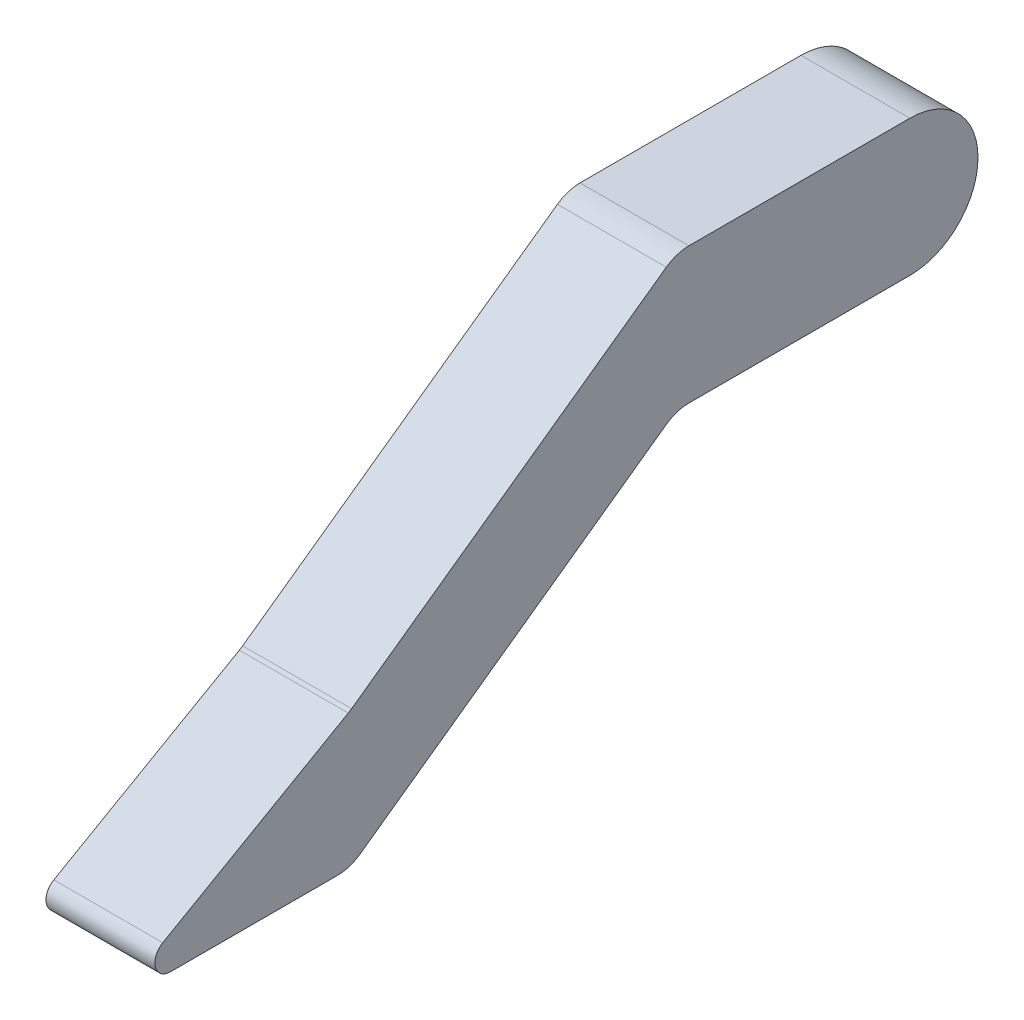
SolidWorks part; units mm, degrees
material "Oak"
ref_plane "Front Plane" through (0, 0, 0) normal (0, 0, 1) x (1, 0, 0)
ref_plane "Top Plane" through (0, 0, 0) normal (0, 1, 0) x (1, 0, 0)
ref_plane "Right Plane" through (0, 0, 0) normal (1, 0, 0) x (0, 0, -1)
sketch "Sketch1" plane through (0, 0, 0) normal (1, 0, 0) x (0, 0, -1)
  line L1 (-34.0276, 22.225) -> (38.1, 22.225)
  line L3 (-34.0276, -22.225) -> (38.1, -22.225)
  line L5 (-38.1, 22.225) -> (38.1, -22.225) construction
  line L6 (-38.1, -22.225) -> (38.1, 22.225) construction
  line L7 (-41.413, 19.8568) -> (-144.1571, -53.5863)
  line L8 (-41.413, -24.5932) -> (-141.3666, -96.0416)
  line L10 (-145.237, -54.2786) -> (-205.8028, -88.9201)
  line L11 (-203.2807, -98.4097) -> (-148.7519, -98.4097)
  arc A0 (38.1, -22.225) -> (38.1, 22.225) centre (38.1, 0) ccw
  arc A1 (-41.413, -24.5932) -> (-34.0276, -22.225) centre (-34.0276, -34.925) cw
  arc A2 (-34.0276, 22.225) -> (-41.413, 19.8568) centre (-34.0276, 9.525) ccw
  arc A3 (-145.237, -54.2786) -> (-144.1571, -53.5863) centre (-151.5425, -43.2544) ccw
  arc A4 (-148.7519, -98.4097) -> (-141.3666, -96.0416) centre (-148.7519, -85.7097) ccw
  arc A5 (-205.8028, -88.9201) -> (-203.2807, -98.4097) centre (-203.2807, -93.3297) ccw
  point P0 (0, 0)
  dimension "D3" = 12.7
  dimension "D4" = 12.7
  dimension "D5" = 12.7
  dimension "D6" = 12.7
  dimension "D7" = 5.08
  dimension "D1" = 44.45
  dimension "D2" = 76.2
extrude "Boss-Extrude1" add sketch "Sketch1" along normal mid plane 35.56
